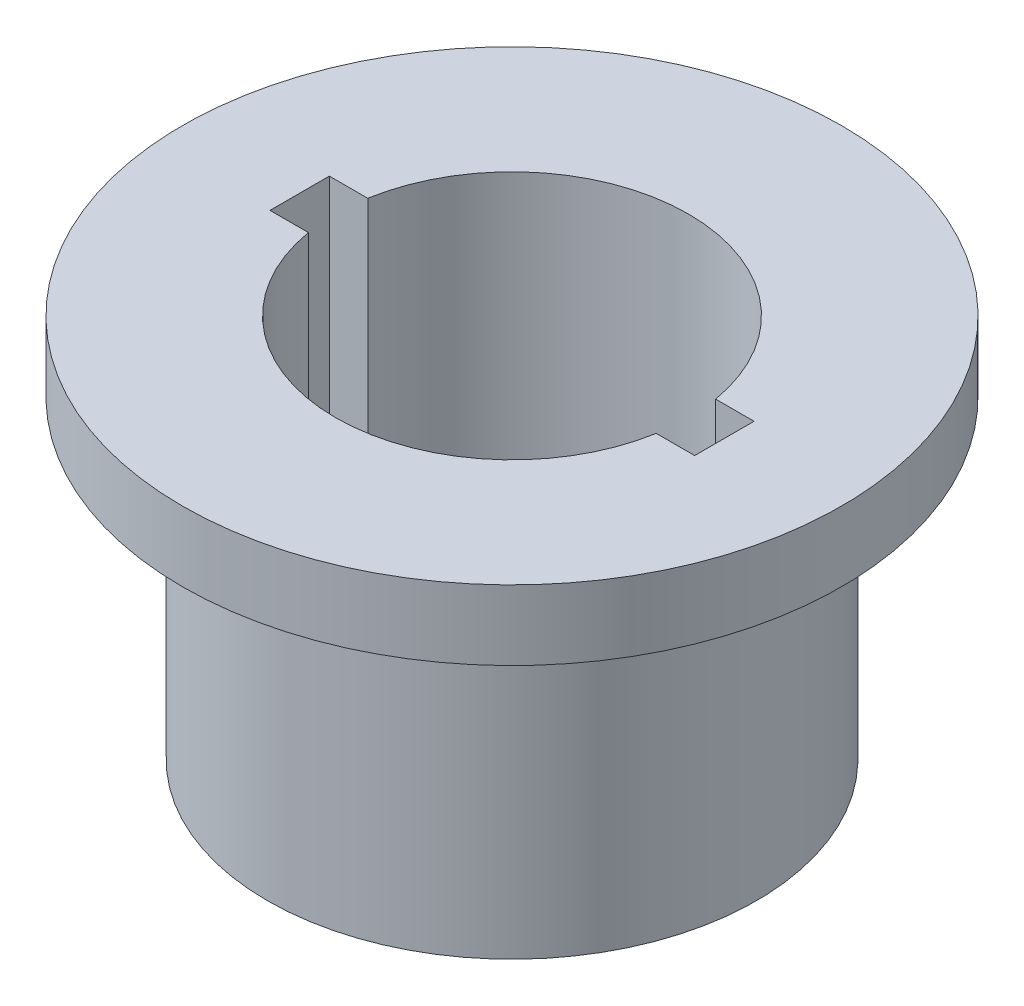
SolidWorks part; units mm, degrees
ref_plane "Front Plane" through (0, 0, 0) normal (0, 0, 1) x (1, 0, 0)
ref_plane "Top Plane" through (0, 0, 0) normal (0, 1, 0) x (1, 0, 0)
ref_plane "Right Plane" through (0, 0, 0) normal (1, 0, 0) x (0, 0, -1)
sketch "Sketch1" plane through (0, 0, 0) normal (0, 1, 0) x (1, 0, 0)
  line L0 (-11.5308, 0) -> (12.1307, 0) construction
  line L1 (-6.078, 0.85) -> (-4.978, 0.85)
  line L2 (-6.078, 0.85) -> (-6.078, -0.85)
  line L3 (-6.078, -0.85) -> (-4.978, -0.85)
  line L4 (6.078, 0.85) -> (6.078, -0.85)
  line L5 (0, 9.5207) -> (0, -9.1962) construction
  line L6 (4.978, 0.85) -> (6.078, 0.85)
  line L7 (4.978, -0.85) -> (6.078, -0.85)
  arc A0 (-4.978, -0.85) -> (4.978, -0.85) centre (0, 0) ccw
  circle A1 centre (0, 0) radius 7
  arc A2 (4.978, 0.85) -> (-4.978, 0.85) centre (0, 0) ccw
  point P12 (6.078, 0)
  dimension "D1" = 10.1
  dimension "D4" = 14
  dimension "D2" = 1.7
  dimension "D3" = 1.1
extrude "Boss-Extrude1" add sketch "Sketch1" along normal blind 11
sketch "Sketch2" plane through (0, 11, 0) normal (0, 1, 0) x (1, 0, 0)
  circle A0 centre (0, 0) radius 7 construction
  circle A1 centre (0, 0) radius 7
  circle A2 centre (0, 0) radius 9.4331
extrude "Boss-Extrude2" add sketch "Sketch2" against normal blind 2
